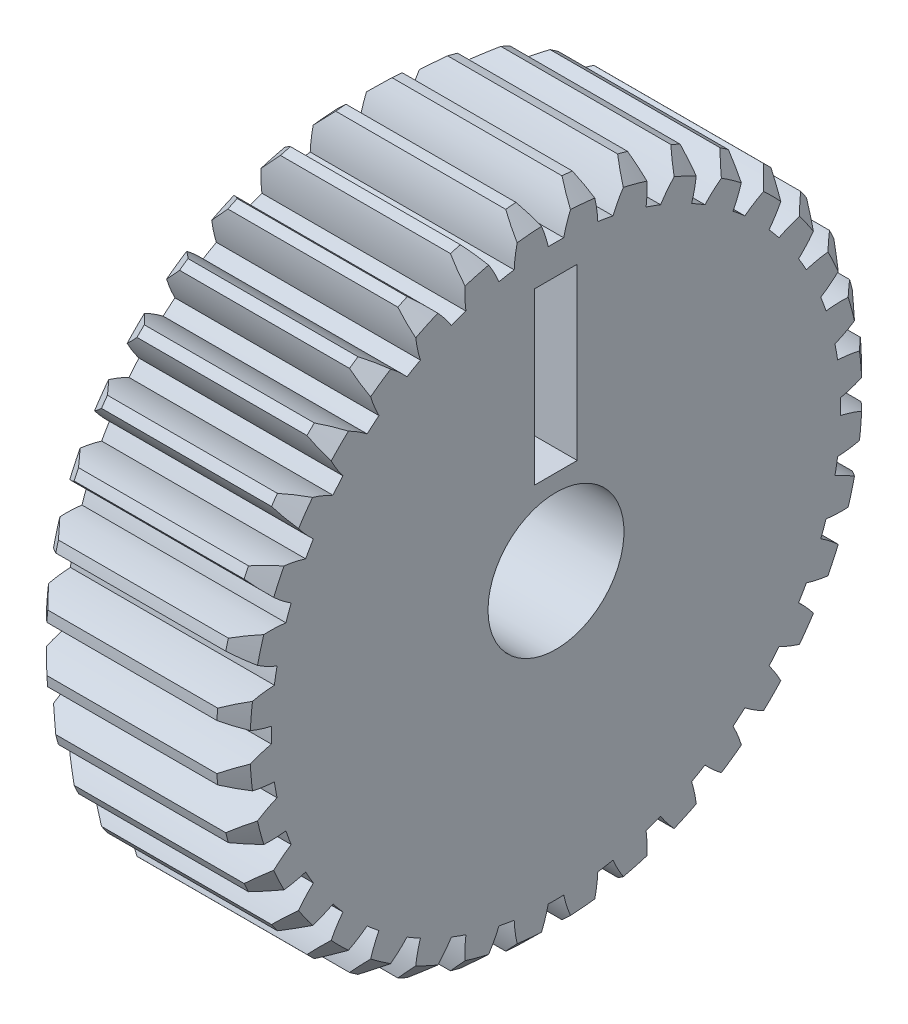
SolidWorks part; units mm, degrees
ref_plane "Plane1" through (0, 0, 0) normal (0, 0, 1) x (1, 0, 0)
ref_plane "Plane2" through (0, 0, 0) normal (0, 1, 0) x (1, 0, 0)
ref_plane "Plane3" through (0, 0, 0) normal (1, 0, 0) x (0, 0, -1)
sketch "HoldingSke" plane through (0, 0, 0) normal (0, 1, 0) x (1, 0, 0)
  line L0 (0, 0) -> (0.809, -0.5878)
  line L1 (-15, 0) -> (100, 0) construction
  line L2 (0, 0) -> (-2.1039, 2.3779)
  line L3 (0, 0) -> (-11.863, 4.5341)
  line L4 (0, 0) -> (6.9867, 5.0761)
  line L5 (0, 0) -> (-16.8652, -6.2902)
  line L6 (0, 0) -> (-9.9476, -6.7116)
  line L7 (-2.1039, 2.3779) -> (1.7711, 19.9584)
  line L8 (-76.2, 54.61) -> (-74.8, 54.61)
  line L9 (-71.009, 38.7566) -> (-53.1078, 45.2721)
  line L10 (-76.2, 71.12) -> (104.1128, 71.12)
  line L11 (0, 0) -> (-12, 0)
  line L12 (-76.2, 101.6) -> (-76.162, 101.6)
  line L13 (24.9733, 27.94) -> (52.9518, 28.4284)
  line L14 (24.9733, 27.94) -> (24.9743, 27.94)
  line L15 (24.9733, 27.94) -> (100.4006, 29.5858)
  line L16 (-63.627, -1) -> (-12.827, -1)
  circle A0 centre (0, 0) radius 4
  circle A1 centre (0, 0) radius 7.5
  circle A2 centre (0, 0) radius 7.5
  circle A3 centre (0, 0) radius 4
  dimension "MHD" = 15
  dimension "Hub_dia" = 15
  dimension "Bore" = 8
  dimension "MBD" = 8
  dimension "Num_teeth" = 36
  dimension "Pitch" = 1
  dimension "Overall_len" = 18
  dimension "Show_teeth" = 36
  dimension "Thickness" = 12
  dimension "OAL" = 18.0025
  dimension "T_dim" = 1.4
  dimension "Ap" = 20
  dimension "H" = 19.05
  dimension "Pitch_radius" = 180.3128
  dimension "Width" = 12
  dimension "Backlash" = 0.038
  dimension "Addendum_fac" = 1
  dimension "Dedendum_fac" = 1.25
  dimension "Clearance_fac" = 0.25
  dimension "Dedendum_add" = 0.001
  dimension "Module" = 1
sketch "BasProSke" plane through (0, 0, 0) normal (0, 1, 0) x (1, 0, 0)
  line L0 (-10, 0) -> (60, 0) construction
  line L1 (0, 0) -> (0, 19)
  line L2 (0, 0) -> (12, 0)
  line L3 (12, 0) -> (12, 19)
  line L4 (12, 19) -> (0, 19)
  dimension "Thickness" = 12
  dimension "Diameter" = 38
revolve "Base-Revolve" add sketch "BasProSke" angle 360 about L0
chamfer "Chamfer1" distance 1 angle 45 2 edges at (12, 0, 19) (0, 0, 19)
sketch "TooCutSke" plane through (0, 0, 0) normal (1, 0, 0) x (0, 0, -1)
  line L1 (0, 0) -> (0, 107) construction
  line L2 (0, 0) -> (-0.8516, 17.9798) construction
  line L3 (0, 0) -> (-3.1351, 35.8344) construction
  line L4 (-0.8516, 17.9798) -> (-1.5676, 17.9172) construction
  arc A0 (0.4547, 16.7428) -> (-0.4547, 16.7428) centre (0, 0) ccw
  arc A1 (1.3689, 18.9761) -> (-1.3689, 18.9761) centre (0, 0) ccw
  circle A2 centre (0, 0) radius 18 construction
  circle A3 centre (0, 0) radius 16.9145 construction
  arc A4 (-0.4547, 16.7428) -> (-1.3689, 18.9761) centre (-7.4808, 15.1702) ccw
  arc A5 (1.3689, 18.9761) -> (0.4547, 16.7428) centre (7.4808, 15.1702) ccw
  dimension "Root_dia" = 33.498
  dimension "Overcut_dia" = 38.0508
  dimension "Pitch_dia" = 36
  dimension "Base_dia" = 33.8289
  dimension "Flank_rad" = 7.2
  dimension "Half_ang" = 5
  dimension "Half_CT" = 0.7186
extrude "ToothCut" cut sketch "TooCutSke" along normal through all
pattern_circular "TeethCuts" count 36 every 10 about axis through (-10, 0, 0) along (1, 0, 0) of "ToothCut"
sketch "HubNeaOneSke" plane through (0, 0, 0) normal (-1, 0, 0) x (0, 0, 1)
  circle A0 centre (0, 0) radius 7.5
  dimension "Diameter" = 15
extrude "HubNearOne" add sketch "HubNeaOneSke" along normal blind 6.0025
sketch "BorSke" plane through (0, 0, 0) normal (1, 0, 0) x (0, 0, -1)
  circle A0 centre (0, 0) radius 4
  dimension "Diameter" = 8
extrude "Bore" cut sketch "BorSke" along normal mid plane 36.005
sketch "KeySke" plane through (0, 0, 0) normal (1, 0, 0) x (0, 0, -1)
  line L0 (-1.5, 0) -> (-1.5, 5.4)
  line L1 (-1.5, 5.4) -> (1.5, 5.4)
  line L2 (1.5, 5.4) -> (1.5, 0)
  line L3 (0, 0) -> (0, 34) construction
  line L4 (-1.5, 0) -> (1.5, 0)
  dimension "Offset" = 5.4
  dimension "Width" = 3
extrude "Keyway" [suppressed] cut sketch "KeySke" along normal mid plane 36.005
sketch "Sketch2" plane through (12, 0, 0) normal (1, 0, 0) x (0, 0, -1)
  line L1 (-1.25, 5) -> (1.25, 5)
  line L2 (-1.25, 5) -> (-1.25, 15)
  line L3 (-1.25, 15) -> (1.25, 15)
  line L4 (1.25, 5) -> (1.25, 15)
  point P4 (0, 5)
  dimension "D1" = 10
  dimension "D2" = 2.5
  dimension "D3" = 5
extrude "Rotation Mark" cut sketch "Sketch2" against normal blind 5
equation "' \"Module@HoldingSke\" = 6.35"
equation "' \"Num_teeth@HoldingSke\" = 12"
equation "' \"Ap@HoldingSke\" =  20"
equation "' \"Ap@HoldingSke\" = 20"
equation "' \"Width@HoldingSke\" = 0.5 * 25.4"
equation "' \"Hub_dia@HoldingSke\"= 1 * 25.4"
equation "' \"Hub_dia@HoldingSke\" = 1 * 25.4"
equation "' \"Overall_len@HoldingSke\" = 1.0 * 25.4"
equation "' \"Bore@HoldingSke\" = 0.75 * 25.4"
equation "' \"T_dim@HoldingSke\" = 0.1 * 25.4"
equation "' \"Width@KeySke\" = 0.25 * 25.4"
equation "' \"Show_teeth@HoldingSke\" = 13"
equation "' \"Backlash@HoldingSke\" = 0.009 * 25.4"
equation "' \"Addendum_fac@HoldingSke\" = 1.0"
equation "' \"Dedendum_fac@HoldingSke\" = 1.25"
equation "' \"Dedendum_add@HoldingSke\" = 0.00005 * 25.4"
equation "' \"Clearance_fac@HoldingSke\" = 0.25"
equation "\"Pitch@HoldingSke\" = 1 / \"Module@HoldingSke\""
equation "\"Overcut_dia@TooCutSke\" = (\"Num_teeth@HoldingSke\" + 2 * \"Addendum_fac@HoldingSke\") / \"Pitch@HoldingSke\" + 0.002 * 25.4"
equation "\"Pitch_dia@TooCutSke\" = \"Num_teeth@HoldingSke\" / \"Pitch@HoldingSke\""
equation "\"Base_dia@TooCutSke\" = \"Num_teeth@HoldingSke\" / \"Pitch@HoldingSke\" * cos((\"Ap@HoldingSke\"  * 3.14159265 / 180))"
equation "\"Root_dia@TooCutSke\" = (\"Num_teeth@HoldingSke\" + 2) / \"Pitch@HoldingSke\" - 2 * (\"Addendum_fac@HoldingSke\" + \"Dedendum_fac@HoldingSke\") / \"Pitch@HoldingSke\" - \"Dedendum_add@HoldingSke\" * 2"
equation "\"Half_ang@TooCutSke\" = 180 / \"Num_teeth@HoldingSke\""
equation "\"Half_CT@TooCutSke\" = \"Num_teeth@HoldingSke\" / \"Pitch@HoldingSke\" * sin((3.14159265 / 2 / \"Num_teeth@HoldingSke\")) / 2 - 7 * \"Backlash@HoldingSke\" / 4"
equation "\"Flank_rad@TooCutSke\" = \"Num_teeth@HoldingSke\" / \"Pitch@HoldingSke\" / 5"
equation "\"Thickness@HoldingSke\" = \"Width@HoldingSke\""
equation "\"OAL@HoldingSke\" = \"Thickness@HoldingSke\""
equation "\"MHD@HoldingSke\" = (\"Num_teeth@HoldingSke\" + 2) / \"Pitch@HoldingSke\" - 2 * (\"Addendum_fac@HoldingSke\" + \"Dedendum_fac@HoldingSke\")  / \"Pitch@HoldingSke\" - \"Dedendum_add@HoldingSke\" * 2"
equation "\"MBD@HoldingSke\" = (\"Num_teeth@HoldingSke\" + 2) / \"Pitch@HoldingSke\" - 2 * (\"Addendum_fac@HoldingSke\" + \"Dedendum_fac@HoldingSke\")  / \"Pitch@HoldingSke\" - \"Dedendum_add@HoldingSke\" * 2 - 0.002 * 25.4"
equation "\"MHD@HoldingSke\" = ((sgn( \"MHD@HoldingSke\" - \"Hub_dia@HoldingSke\" )-1)*( \"MHD@HoldingSke\" - \"Hub_dia@HoldingSke\" ))/-2+ \"Hub_dia@HoldingSke\""
equation "\"MBD@HoldingSke\" = ((sgn( \"MBD@HoldingSke\" - \"Bore@HoldingSke\" )-1)*( \"MBD@HoldingSke\" - \"Bore@HoldingSke\" ))/-2+ \"Bore@HoldingSke\""
equation "\"OAL@HoldingSke\" = ((sgn( \"OAL@HoldingSke\" - \"Overall_len@HoldingSke\" )+1)*( \"OAL@HoldingSke\" - \"Overall_len@HoldingSke\" ))/2 + \"Overall_len@HoldingSke\" + 0.000002 * 25.4"
equation "\"Num_teeth@TeethCuts\" = int( \"Show_teeth@HoldingSke\" ) + 1"
equation "\"Num_teeth@TeethCuts\" = ((sgn( \"Num_teeth@TeethCuts\" - \"Num_teeth@HoldingSke\" )-1)*( \"Num_teeth@TeethCuts\" - \"Num_teeth@HoldingSke\" ))/-2+ \"Num_teeth@HoldingSke\""
equation "\"Num_teeth@TeethCuts\" = ((sgn( \"Num_teeth@TeethCuts\" - 2.0)+1)*( \"Num_teeth@TeethCuts\" - 2.0))/2 +2.0"
equation "\"Angle@TeethCuts\" = 360.0 / \"Num_teeth@HoldingSke\""
equation "\"Diameter@BasProSke\" = (\"Num_teeth@HoldingSke\" + 2 * \"Addendum_fac@HoldingSke\") / \"Pitch@HoldingSke\""
equation "\"Thickness@BasProSke\"  = \"Thickness@HoldingSke\""
equation "' \"Fillet_rad@BasProSke\" =  \"Thickness@HoldingSke\" * 0.05"
equation "' \"Fillet_rad@BasProSke\" = \"Thickness@HoldingSke\" * 0.05"
equation "\"MHD@HoldingSke\" = ((sgn( \"MHD@HoldingSke\" - \"Root_dia@TooCutSke\" )-1)*( \"MHD@HoldingSke\" - \"Root_dia@TooCutSke\" ))/-2+ \"Root_dia@TooCutSke\""
equation "\"Diameter@HubNeaOneSke\" = \"MHD@HoldingSke\""
equation "\"Length@HubNearOne\" = \"OAL@HoldingSke\" - \"Thickness@BasProSke\""
equation "\"Diameter@BorSke\" = \"MBD@HoldingSke\""
equation "\"D1@Bore\" = \"OAL@HoldingSke\" * 2.0"
equation "\"D1@Keyway\" = \"OAL@HoldingSke\" * 2.0"
equation "\"Offset@KeySke\" = \"T_dim@HoldingSke\" + \"MBD@HoldingSke\" / 2.0"
